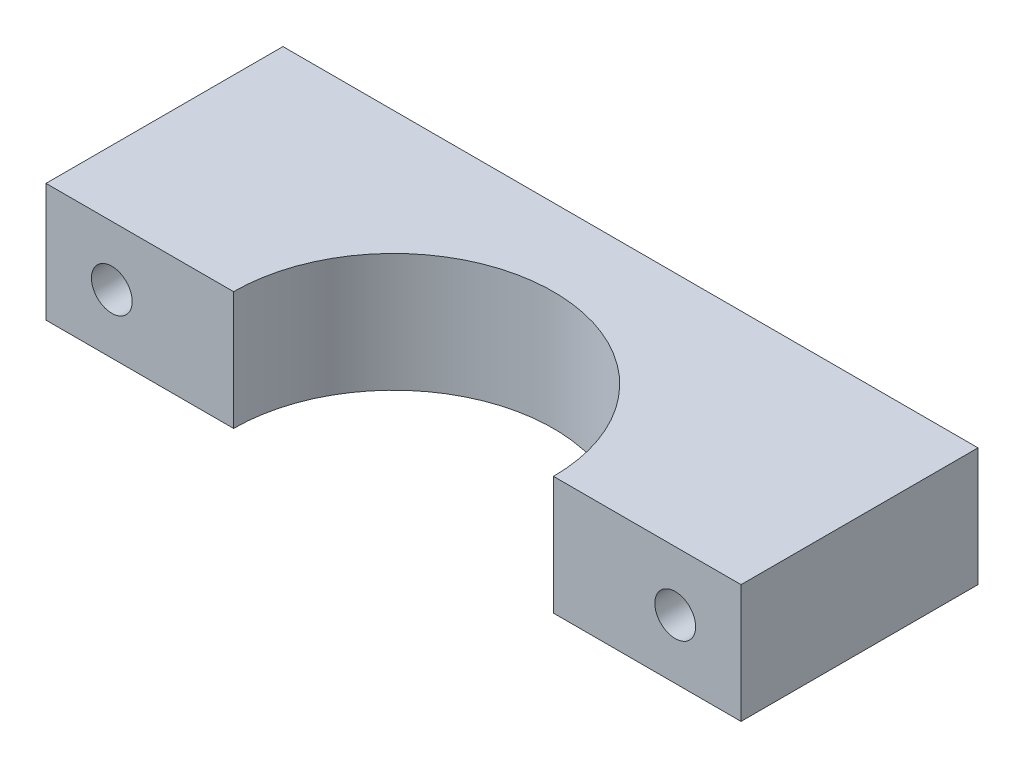
SolidWorks part; units mm, degrees
ref_plane "Front Plane" through (0, 0, 0) normal (0, 0, 1) x (1, 0, 0)
ref_plane "Top Plane" through (0, 0, 0) normal (0, 1, 0) x (1, 0, 0)
ref_plane "Right Plane" through (0, 0, 0) normal (1, 0, 0) x (0, 0, -1)
sketch "Sketch1" plane through (0, 0, 0) normal (0, 1, 0) x (1, 0, 0)
  line L3 (12.15, 0) -> (26.4, 0)
  line L6 (0, -8.3817) -> (0, 8.3817) construction
  line L7 (-12.15, 0) -> (-26.4, 0)
  line L11 (26.4, 18) -> (-26.4, 18)
  line L13 (26.4, 0) -> (26.4, 18)
  line L14 (-26.4, 0) -> (-26.4, 18)
  arc A0 (12.15, 0) -> (-12.15, 0) centre (0, 0) ccw
  point P6 (0, 0)
  point P11 (0, 5)
  point P12 (0, 0)
  dimension "D1" = 24.3
  dimension "D2" = 18
  dimension "D3" = 14.25
extrude "Boss-Extrude1" add sketch "Sketch1" along normal blind 9
sketch "Sketch2" plane through (0, 0, 0) normal (0, 0, 1) x (1, 0, 0)
  line L4 (12.15, 0) -> (26.4, 0)
  line L5 (26.4, 0) -> (26.4, 9)
  line L6 (26.4, 9) -> (12.15, 9)
  line L7 (12.15, 9) -> (12.15, 0)
  line L8 (12.15, 0) -> (26.4, 0)
  line L10 (26.4, 9) -> (12.15, 9)
  line L11 (12.15, 9) -> (12.15, 0)
  line L12 (26.4, 0) -> (26.4, 9)
  circle A0 centre (21.4, 4.5) radius 1.55
  dimension "D2" = 3.1
  dimension "D3" = 5
  dimension "D1" = 0
extrude "Cut-Extrude1" cut sketch "Sketch2" against normal through all contours A0
mirror "Mirror1" about plane through (0, 0, 0) normal (1, 0, 0) of "Cut-Extrude1"
